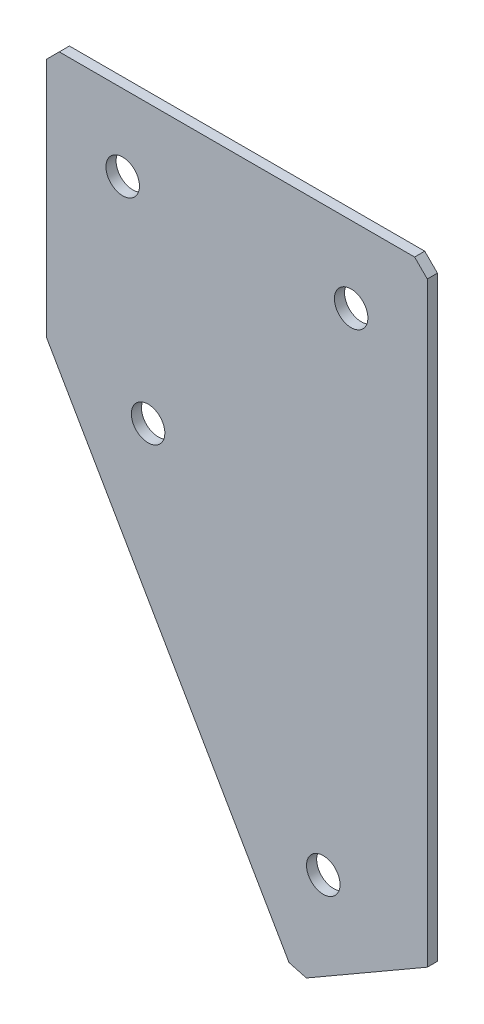
SolidWorks part; units mm, degrees
material "Простая углеродистая сталь"
ref_plane "Спереди" through (0, 0, 0) normal (0, 0, 1) x (1, 0, 0)
ref_plane "Сверху" through (0, 0, 0) normal (0, 1, 0) x (1, 0, 0)
ref_plane "Справа" through (0, 0, 0) normal (1, 0, 0) x (0, 0, -1)
sketch "Эскиз3" plane through (0, 0, 0) normal (0, 0, -1) x (1, 0, 0)
  line L0 (0, 0) -> (75, 0)
  line L1 (75, 0) -> (75, 119.9038)
  line L2 (0, 0) -> (0, 50)
  line L3 (0, 50) -> (49.0192, 134.9038)
  line L4 (49.0192, 134.9038) -> (75, 119.9038)
  dimension "D1" = 75
  dimension "D2" = 50
  dimension "D3" = 30
  dimension "D4" = 60
  dimension "D5" = 119.9038
extrude "Бобышка-Вытянуть1" add sketch "Эскиз3" along normal blind 2
hole_wizard "Отверстие с зазором M61" positions "Эскиз4" profile "Эскиз5" hole size "M6" standard "DIN" end condition through all
sketch "Эскиз4" plane through (0, 0, -2) normal (0, 0, -1) x (1, 0, 0)
  line L0 (20, 54.641) -> (54.5096, 114.4134) construction
  line L2 (49.0192, 134.9038) -> (0, 50) construction
  line L3 (15, 15) -> (60, 15) construction
  line L5 (0, 0) -> (75, 0) construction
  line L6 (0, 50) -> (0, 0) construction
  line L7 (75, 0) -> (75, 119.9038) construction
  line L8 (75, 119.9038) -> (49.0192, 134.9038) construction
  line L9 (20, 54.641) -> (0, 20) construction
  point P0 (15, 15)
  point P2 (60, 15)
  point P4 (20, 54.641)
  point P6 (54.5096, 114.4134)
  dimension "D1" = 15
  dimension "D2" = 15
  dimension "D3" = 15
  dimension "D4" = 15
  dimension "D5" = 15
  dimension "D6" = 40
  dimension "D7" = 69.0192
  dimension "D8" = 45
sketch "Эскиз5" plane through (15, -15, -2) normal (1, 0, 0) x (0, 1, 0)
  line L0 (0, 0) -> (0, 2)
  line L1 (0, 2) -> (3.3, 2)
  line L2 (3.3, 2) -> (3.3, 0)
  line L5 (3.3, 0) -> (0, 0)
  line L11 (0, -6.35) -> (0, 107.95) construction
  dimension "Диаметр сквозного отверстия" = 6.6
  dimension "Глубина сквозного отверстия" = 2
chamfer "Фаска1" distance 2.5 distance2 2.5 3 edges at (49.0192, -134.9038, -1) (75, 0, -1) (0, 0, -1)
